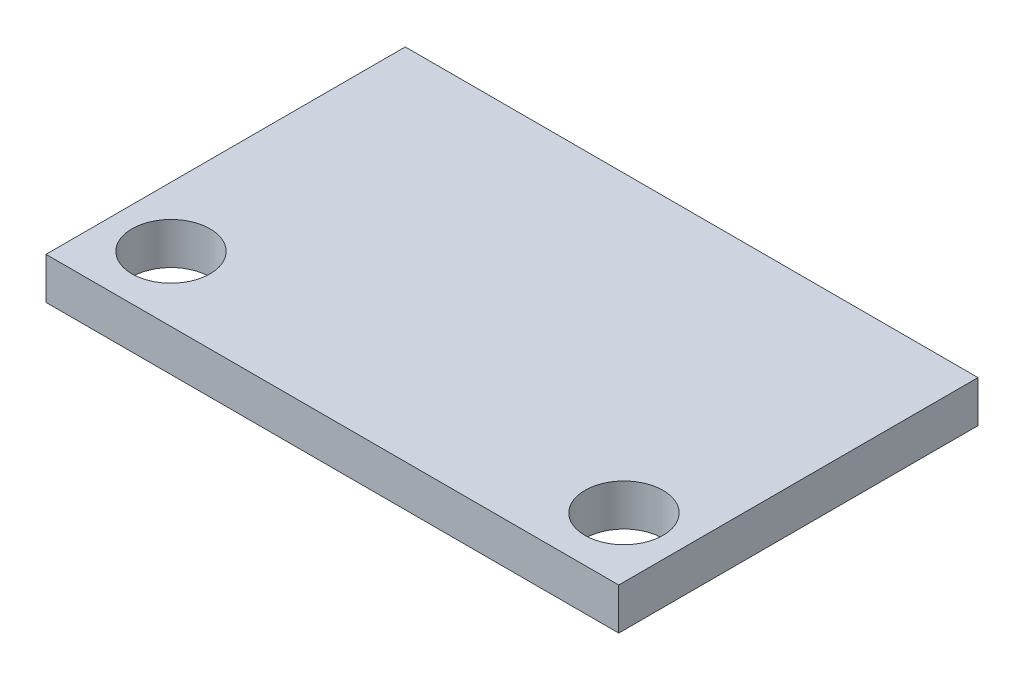
SolidWorks part; units mm, degrees
ref_plane "前视基准面" through (0, 0, 0) normal (0, 0, 1) x (1, 0, 0)
ref_plane "上视基准面" through (0, 0, 0) normal (0, 1, 0) x (1, 0, 0)
ref_plane "右视基准面" through (0, 0, 0) normal (1, 0, 0) x (0, 0, -1)
sketch "草图1" plane through (0, 0, 0) normal (0, 1, 0) x (1, 0, 0)
  line L1 (-11, -6.9) -> (11, -6.9)
  line L2 (-11, -6.9) -> (-11, 6.9)
  line L3 (-11, 6.9) -> (11, 6.9)
  line L4 (11, -6.9) -> (11, 6.9)
  line L5 (-11, -6.9) -> (11, 6.9) construction
  line L6 (-11, 6.9) -> (11, -6.9) construction
  circle A0 centre (-8.7, -4.4) radius 1.5
  circle A1 centre (8.7, -4.4) radius 1.5
  point P0 (0, 0)
  point P10 (0, 0)
  dimension "D3" = 3
  dimension "D4" = 3
  dimension "D5" = 2.3
  dimension "D6" = 2.3
  dimension "D7" = 2.5
  dimension "D1" = 22
  dimension "D2" = 13.8
extrude "凸台-拉伸1" add sketch "草图1" along normal blind 1.6
